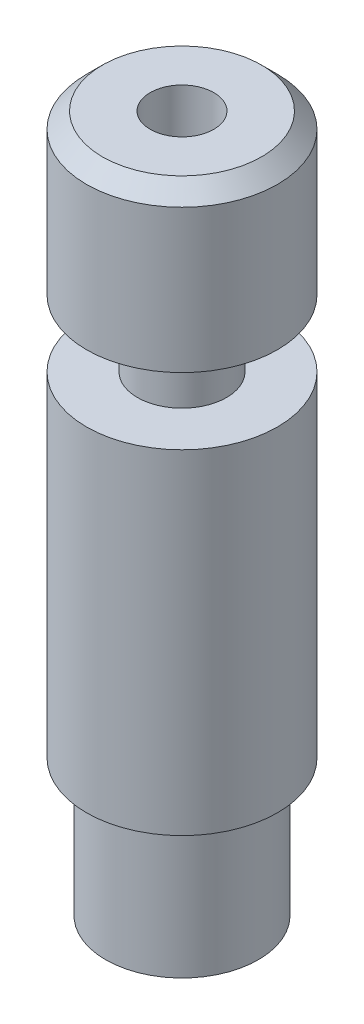
SolidWorks part; units mm, degrees
material "AISI 316 Annealed Stainless Steel Bar (SS)"
ref_plane "Front Plane" through (0, 0, 0) normal (0, 0, 1) x (1, 0, 0)
ref_plane "Top Plane" through (0, 0, 0) normal (0, 1, 0) x (1, 0, 0)
ref_plane "Right Plane" through (0, 0, 0) normal (1, 0, 0) x (0, 0, -1)
sketch "Sketch1" plane through (0, 0, 0) normal (0, 0, 1) x (1, 0, 0)
  line L0 (0, 11.0943) -> (0, -11.0943) construction
  line L1 (1, -10.6943) -> (1, 11.0943)
  line L2 (1, 11.0943) -> (2.5, 11.0943)
  line L3 (3, 10.5943) -> (3, 6.0943)
  line L4 (3, 6.0943) -> (1.4, 6.0943)
  line L5 (1.4, 6.0943) -> (1.4, 3.9943)
  line L6 (1.4, 3.9943) -> (3, 3.9943)
  line L7 (2.4, -10.8057) -> (2.4, -6.5057)
  line L8 (1.4, -11.0943) -> (1.9, -11.0943)
  line L9 (2.4, -6.5057) -> (3, -6.5057)
  line L10 (3, -6.5057) -> (3, 3.9943)
  line L11 (2.5, 11.0943) -> (3, 10.5943)
  line L13 (1.4, -11.0943) -> (1, -10.6943)
  line L14 (1.9, -11.0943) -> (2.4, -10.8057)
  point P3 (1, -11.0943)
  point P6 (3, 11.0943)
  dimension "D2" = 1
  dimension "D3" = 7.1
  dimension "D4" = 2.1
  dimension "D5" = 6
  dimension "D6" = 14.8
  dimension "D7" = 4.8
  dimension "D8" = 0.4
  dimension "D12" = 4.3
  dimension "D9" = 3.8
  dimension "D10" = 30
revolve "Revolve1" add sketch "Sketch1" angle 360 about L0
